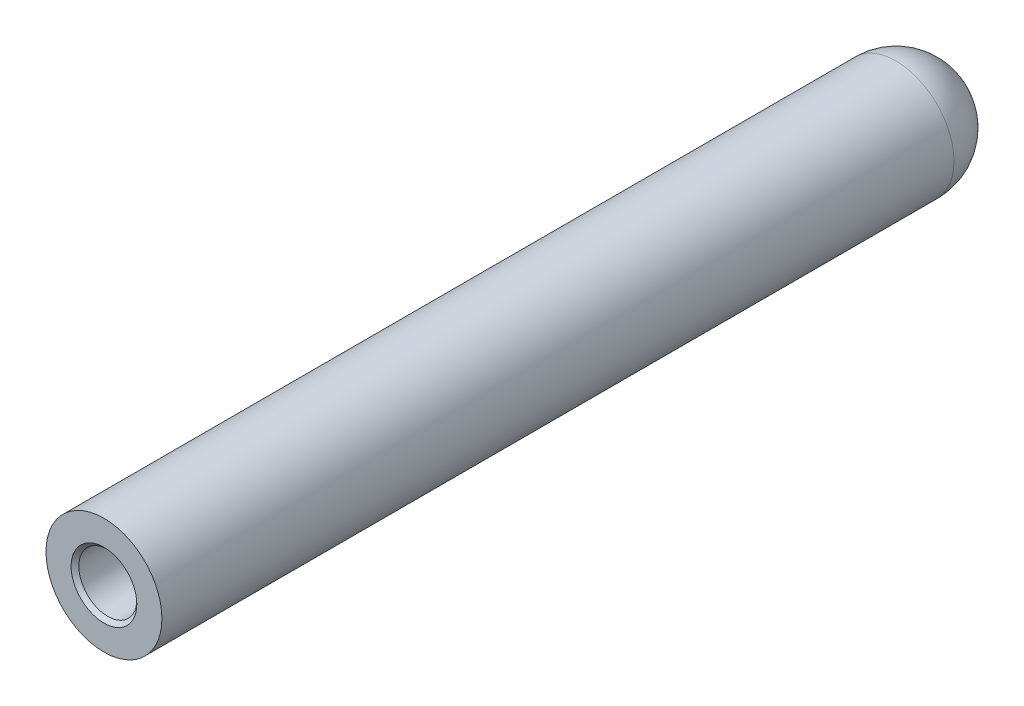
SolidWorks part; units mm, degrees
material "6061-T6 Al"
ref_plane "Front" through (0, 0, 0) normal (0, 0, 1) x (1, 0, 0)
ref_plane "Top" through (0, 0, 0) normal (0, 1, 0) x (1, 0, 0)
ref_plane "Right" through (0, 0, 0) normal (1, 0, 0) x (0, 0, -1)
sketch "Sketch1" plane through (0, 0, 0) normal (0, 0, 1) x (1, 0, 0)
  circle A0 centre (0, 0) radius 9.525
  dimension "D1" = 19.05
extrude "Boss-Extrude1" add sketch "Sketch1" along normal blind 139.7
fillet "Fillet1" radius 9.525 1 edges at (9.525, 0, 0)
hole_wizard "3/8-16 Tapped Hole1" positions "Sketch3" profile "Sketch2" tap size "3/8-16" standard "Ansi Inch"
sketch "Sketch3" plane through (0, 0, 139.7) normal (0, 0, 1) x (1, 0, 0)
  point P0 (0, 0)
sketch "Sketch2" plane through (0, 0, 139.7) normal (1, 0, 0) x (0, -1, 0)
  line L0 (0, 0) -> (0, 42.0849)
  line L1 (0, 42.0849) -> (3.9687, 39.7002)
  line L2 (3.9687, 39.7002) -> (3.9687, 31.75)
  line L3 (3.9687, 31.75) -> (4.7625, 31.75)
  line L5 (4.7625, 31.75) -> (4.7625, 0.635)
  line L6 (4.7625, 0.635) -> (5.3975, 0)
  line L7 (5.3975, 0) -> (0, 0)
  line L8 (-4.7625, 0.635) -> (-5.3975, 0) construction
  line L10 (0, 42.0849) -> (-3.9688, 39.7002) construction
  line L11 (0, -6.35) -> (0, 107.95) construction
  dimension "Tap Drill Dia." = 7.9375
  dimension "Tap Drill Depth" = 39.7002
  dimension "Thread Major Dia." = 9.525
  dimension "Thread Depth" = 31.75
  dimension "Near C'Sink Dia." = 10.795
  dimension "Near C'Sink Angle" = 90
  dimension "Drill Angle" = 118
